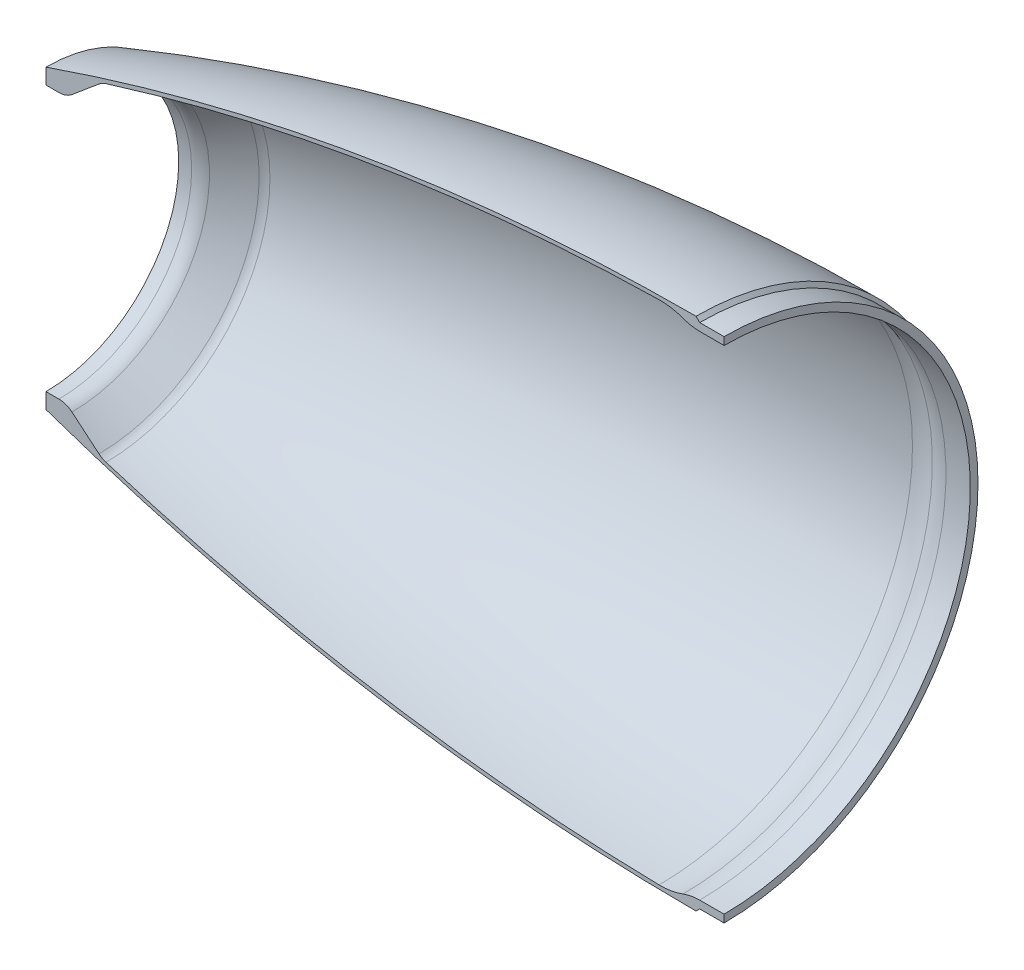
SolidWorks part; units mm, degrees
ref_plane "Front Plane" through (0, 0, 0) normal (0, 0, 1) x (1, 0, 0)
ref_plane "Top Plane" through (0, 0, 0) normal (0, 1, 0) x (1, 0, 0)
ref_plane "Right Plane" through (0, 0, 0) normal (1, 0, 0) x (0, 0, -1)
sketch "Sketch1" plane through (0, 0, 0) normal (0, 0, 1) x (1, 0, 0)
  line L4 (0, 0) -> (-304.8, 0) construction
  line L9 (0, 76.975) -> (0, 0) construction
  line L10 (0, 80.518) -> (50.8, 80.518) construction
  line L11 (-203.2, 46.355) -> (-203.2, 41.4909)
  line L12 (-203.2, 41.4909) -> (-199.1612, 41.4909)
  line L14 (-195.0795, 42.9765) -> (-186.6413, 50.057)
  line L15 (1.143, 79.375) -> (8.763, 79.375)
  line L16 (0, 80.518) -> (1.143, 79.375)
  line L17 (1.143, 76.975) -> (8.763, 76.975)
  line L18 (8.763, 76.975) -> (8.763, 79.375)
  arc A4 (0, 80.518) -> (-203.2, 46.355) centre (0, -540.8758) ccw
  arc A5 (-11.557, 79.2103) -> (-184.4481, 51.2553) centre (0, -540.8758) ccw
  arc A6 (0, 79.318) -> (-202.8076, 45.221) centre (0, -540.8758) ccw construction
  arc A10 (-4.0446, 77.9175) -> (1.143, 76.975) centre (1.143, 91.722) ccw
  arc A11 (-199.1612, 41.4909) -> (-195.0795, 42.9765) centre (-199.1612, 47.8409) ccw
  arc A12 (-184.4481, 51.2553) -> (-186.6413, 50.057) centre (-182.5596, 45.1926) ccw
  arc A13 (-11.557, 79.2103) -> (-4.0446, 77.9175) centre (-11.1791, 58.9324) cw
  point P8 (-57.2734, -19.8104)
  point P9 (0, 313.4439)
  point P10 (-150.9565, 274.6984)
  point P21 (-196.85, 41.4909)
  dimension "D7" = 6.35
  dimension "D10" = 6.35
  dimension "D17" = 5.1876
  dimension "D8" = 140
  dimension "D16" = 12.7
  dimension "D1" = 161.036
  dimension "D2" = 50.8
  dimension "D3" = 203.2
  dimension "D4" = 92.71
  dimension "D6" = 82.9818
  dimension "D9" = 304.8
  dimension "D12" = 7.62
  dimension "D13" = 158.75
  dimension "D14" = 45
  dimension "D15" = 2.4
  dimension "D5" = 1.2
revolve "Revolve1" add sketch "Sketch1" angle 180 about L4
